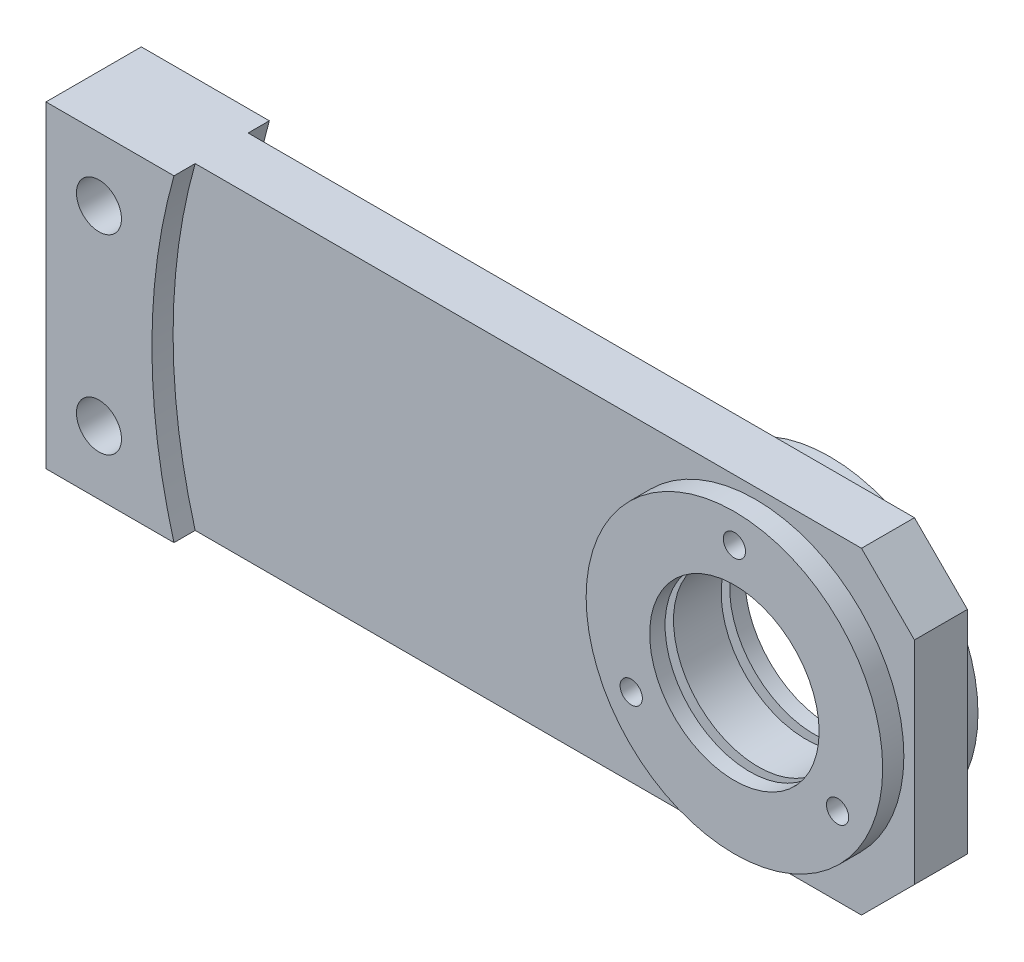
SolidWorks part; units mm, degrees
material "1.0037 (S235JR)"
ref_plane "Front Plane" through (0, 0, 0) normal (0, 0, 1) x (1, 0, 0)
ref_plane "Top Plane" through (0, 0, 0) normal (0, 1, 0) x (1, 0, 0)
ref_plane "Right Plane" through (0, 0, 0) normal (1, 0, 0) x (0, 0, -1)
sketch "Sketch1" plane through (0, 0, 0) normal (0, 0, 1) x (1, 0, 0)
  line L0 (-80, 0) -> (80, 0) construction
  line L5 (80, 30) -> (-80, 30)
  line L6 (80, 30) -> (80, -30)
  line L7 (80, -30) -> (-80, -30)
  line L8 (-80, 30) -> (-80, -30)
  line L9 (80, 30) -> (-80, -30) construction
  line L10 (80, -30) -> (-80, 30) construction
  circle A2 centre (-70, 18) radius 4.25
  circle A3 centre (-70, -18) radius 4.25
  circle A4 centre (50, 0) radius 16
  circle A5 centre (50, 0) radius 22.5 construction
  point P0 (0, 0)
  point P14 (50, 22.5)
  dimension "D5" = 8.5
  dimension "D6" = 8.5
  dimension "D9" = 32
  dimension "D10" = 45
  dimension "D1" = 60
  dimension "D2" = 160
  dimension "D3" = 18
  dimension "D4" = 18
  dimension "D7" = 36
  dimension "D8" = 10
  dimension "D11" = 30
extrude "Boss-Extrude1" add sketch "Sketch1" along normal mid plane 18
sketch "Sketch2" plane through (0, 0, 9) normal (0, 0, 1) x (1, 0, 0)
  line L0 (50, 0) -> (50, 22.5) construction
  dimension "D1" = 22.5
hole_wizard "M5 Tapped Hole1" positions "3DSketch1" profile "Sketch3" tap size "M5" standard "ISO"
sketch3d "3DSketch1"
  point P0 (50, 22.5, 9)
sketch "Sketch3" plane through (50, 22.5, 9) normal (1, 0, 0) x (0, -1, 0)
  line L0 (0, 0) -> (0, 11.2618)
  line L1 (0, 11.2618) -> (2.1, 10)
  line L2 (2.1, 10) -> (2.1, 0)
  line L5 (2.1, 0) -> (0, 0)
  line L10 (0, 11.2618) -> (-2.1, 10) construction
  line L11 (0, -6.35) -> (0, 107.95) construction
  dimension "Tap Drill Dia." = 4.2
  dimension "Tap Drill Depth" = 10
  dimension "Drill Angle" = 118
cosmetic thread "Hole Thread1" parameters "D1"=10, "D2"=5
pattern_circular "CirPattern1" count 3 over 360 about axis through (0, 0, 9) along (0, 0, -1) skipping 1, 2 of "M5 Tapped Hole1"
pattern_circular "CirPattern2" count 3 over 360 about axis through (50, 0, 0) along (0, 0, 1) of "M5 Tapped Hole1"
cosmetic thread "Hole Thread2" parameters "D1"=10, "D2"=5
cosmetic thread "Hole Thread3" parameters "D1"=10, "D2"=5
chamfer "Chamfer1" distance 10 angle 45 2 edges at (80, 30, 0) (80, -30, 0)
ref_plane "Plane1" through (0, 0, 4.5) normal (0, 0, 1) x (1, 0, 0)
sketch "Sketch5" plane through (0, 0, 4.5) normal (0, 0, 1) x (1, 0, 0)
  circle A0 centre (50, 0) radius 16 construction
  circle A1 centre (50, 0) radius 16
  circle A2 centre (50, 0) radius 18.5
  dimension "D1" = 2.5
extrude "Cut-Extrude2" cut sketch "Sketch5" along normal blind 1.6
mirror "Mirror2" about plane through (0, 0, 0) normal (0, 0, 1) of "Cut-Extrude2"
sketch "Sketch4" plane through (0, 0, 9) normal (0, 0, 1) x (1, 0, 0)
  line L0 (-80, -30) -> (70, -30) construction
  line L1 (70, -30) -> (80, -20) construction
  line L2 (80, -20) -> (80, 20) construction
  line L3 (80, 20) -> (70, 30) construction
  line L4 (70, 30) -> (-80, 30) construction
  line L5 (-80, 30) -> (-80, -30) construction
  line L6 (-80, -30) -> (70, -30)
  line L7 (70, -30) -> (80, -20)
  line L8 (80, -20) -> (80, 20)
  line L9 (80, 20) -> (70, 30)
  line L10 (70, 30) -> (-80, 30)
  line L11 (-80, 30) -> (-80, -30)
  circle A0 centre (50, 0) radius 28
  circle A1 centre (50, 0) radius 110
  line M10 (80, -20) -> (80, 20)
  line M11 (80, 20) -> (70, 30)
  line M12 (70, 30) -> (-80, 30)
  line M15 (70, -30) -> (80, -20)
  dimension "D1" = 56
  dimension "D2" = 220
extrude "Cut-Extrude1" cut sketch "Sketch4" against normal blind 4 contours A1 L6 A0 M12 M15 M10 M11
mirror "Mirror1" about plane through (0, 0, 0) normal (0, 0, 1) of "Cut-Extrude1"
fillet "Fillet1" [suppressed] radius 2
